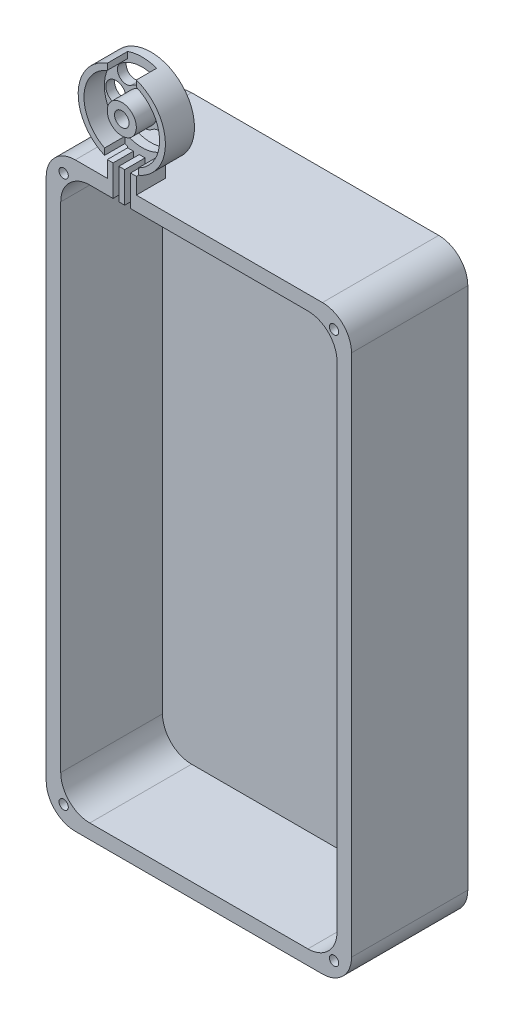
SolidWorks part; units mm, degrees
ref_plane "Front Plane" through (0, 0, 0) normal (0, 0, 1) x (1, 0, 0)
ref_plane "Top Plane" through (0, 0, 0) normal (0, 1, 0) x (1, 0, 0)
ref_plane "Right Plane" through (0, 0, 0) normal (1, 0, 0) x (0, 0, -1)
sketch "Sketch1" plane through (0, 0, 0) normal (0, 0, 1) x (1, 0, 0)
  line L1 (0, 0) -> (105, 0)
  line L2 (0, 0) -> (0, 200)
  line L3 (0, 200) -> (105, 200)
  line L4 (105, 0) -> (105, 200)
  dimension "D1" = 105
  dimension "D2" = 200
extrude "Boss-Extrude1" add sketch "Sketch1" along normal blind 40
sketch "Sketch2" plane through (0, 0, 40) normal (0, 0, 1) x (1, 0, 0)
  line L12 (5, 195) -> (5, 5)
  line L13 (5, 5) -> (100, 5)
  line L14 (100, 5) -> (100, 195)
  line L15 (100, 195) -> (5, 195)
  line L16 (5, 195) -> (5, 5)
  line L17 (5, 5) -> (100, 5)
  line L18 (100, 5) -> (100, 195)
  line L19 (100, 195) -> (5, 195)
  dimension "D1" = 5
extrude "Cut-Extrude1" cut sketch "Sketch2" against normal blind 35
fillet "Fillet1" radius 10 8 edges at (100, 5, 22.5) (105, 0, 20) (0, 0, 20) (5, 5, 22.5) (5, 195, 22.5) (0, 200, 20) (100, 195, 22.5) (105, 200, 20)
sketch "Sketch3" plane through (0, 0, 40) normal (0, 0, 1) x (1, 0, 0)
  line L0 (0, 190) -> (0, 10) construction
  line L1 (95, 200) -> (10, 200) construction
  line L2 (52.5, 200) -> (52.5, 0) construction
  line L3 (10, 0) -> (95, 0) construction
  line L4 (0, 100) -> (105, 100) construction
  line L5 (105, 10) -> (105, 190) construction
  circle A0 centre (6, 194) radius 1.6
  circle A1 centre (99, 194) radius 1.6
  circle A2 centre (99, 6) radius 1.6
  circle A3 centre (6, 6) radius 1.6
  dimension "D1" = 3.2
  dimension "D2" = 6
  dimension "D3" = 6
extrude "Cut-Extrude2" cut sketch "Sketch3" against normal blind 35
sketch "Sketch4" plane through (0, 0, 40) normal (0, 0, 1) x (1, 0, 0)
  line L2 (21, 200) -> (21, 206)
  line L4 (31, 200) -> (31, 206)
  line L5 (0, 190) -> (0, 10) construction
  line L6 (21, 200) -> (31, 200)
  line L7 (95, 200) -> (10, 200) construction
  arc A0 (31, 206) -> (21, 206) centre (26, 220.1421) ccw
  dimension "D4" = 30
  dimension "D1" = 6
  dimension "D2" = 6
  dimension "D3" = 21
  dimension "D5" = 10
extrude "Boss-Extrude2" add sketch "Sketch4" against normal blind 10
sketch "Sketch6" plane through (0, 0, 40) normal (0, 0, 1) x (1, 0, 0)
  circle A0 centre (26, 220.1421) radius 2.5
  dimension "D1" = 5
extrude "Cut-Extrude3" cut sketch "Sketch6" against normal up to surface (10 mm away) up to face at (26, 210.2855, 30)
sketch "Sketch7" plane through (0, 0, 40) normal (0, 0, 1) x (1, 0, 0)
  line L0 (20.966, 234.2722) -> (20.966, 232.1301)
  line L1 (30.966, 232.1562) -> (30.966, 234.2962)
  line L2 (21, 206) -> (21, 208.1421)
  line L3 (31, 206) -> (31, 208.1421)
  circle A0 centre (26, 220.1421) radius 13
  arc A1 (31, 206) -> (21, 206) centre (26, 220.1421) ccw construction
  arc A2 (31, 206) -> (21, 206) centre (26, 220.1421) ccw
  circle A3 centre (26, 220.1421) radius 5
  dimension "D1" = 26
  dimension "D5" = 10
  dimension "D2" = 2.1421
  dimension "D3" = 2.14
  dimension "D4" = 10
extrude "Cut-Extrude5" cut sketch "Sketch7" against normal blind 7 contours A0 A3
sketch "Sketch9" plane through (0, 0, 40) normal (0, 0, 1) x (1, 0, 0)
  line L0 (21, 231.4992) -> (31, 231.4992)
  line L1 (21, 206) -> (31, 206)
  line L2 (21, 231.4992) -> (21, 236.2177)
  line L3 (21, 236.2177) -> (31, 236.2177)
  line L4 (31, 231.4992) -> (31, 236.2177)
  circle A0 centre (26, 220.1421) radius 5 construction
  point P12 (28.9963, 222.2726)
  circle M5 centre (26, 220.1421) radius 13
  arc M24 (31, 206) -> (21, 206) centre (26, 220.1421) ccw
  dimension "D3" = 5
  dimension "D1" = 10
  dimension "D2" = 4.7185
extrude "Cut-Extrude8" cut sketch "Sketch9" against normal blind 7 contours L4 L3 L2 M24 | L0 L4 L2 M5 | L4 L2 M5 M24
sketch "Sketch10" plane through (0, 0, 40) normal (0, 0, 1) x (1, 0, 0)
  line L1 (20.0722, 205.5809) -> (31.7029, 205.5809)
  line L2 (20.0722, 205.5809) -> (20.0722, 209.4312)
  line L3 (20.0722, 209.4312) -> (31.7029, 209.4312)
  line L4 (31.7029, 205.5809) -> (31.7029, 209.4312)
  point P5 (0, 0)
  point P6 (0, 0)
  point P7 (20.0722, 205.7671)
  point P8 (31.7029, 205.5809)
extrude "Cut-Extrude11" cut sketch "Sketch10" against normal blind 7
sketch "Sketch11" plane through (0, 0, 40) normal (0, 0, 1) x (1, 0, 0)
  line L1 (23, 205.7748) -> (25, 205.7748)
  line L2 (23, 205.7748) -> (23, 194.6833)
  line L3 (23, 194.6833) -> (25, 194.6833)
  line L4 (25, 205.7748) -> (25, 194.6833)
  line L6 (27, 205.8743) -> (29, 205.8743)
  line L7 (27, 205.8743) -> (27, 194.718)
  line L8 (27, 194.718) -> (29, 194.718)
  line L9 (29, 205.8743) -> (29, 194.718)
  line L10 (21, 205.5809) -> (21, 200) construction
  line L11 (31, 200) -> (31, 205.5809) construction
  dimension "D1" = 2
  dimension "D2" = 2
  dimension "D3" = 2
  dimension "D4" = 2
  dimension "D5" = 11.0915
  dimension "D6" = 11.1563
extrude "Cut-Extrude12" cut sketch "Sketch11" against normal blind 7
sketch "Sketch12" plane through (0, 0, 30) normal (0, 0, -1) x (-1, 0, 0)
  line L0 (-26, 235.1421) -> (-26, 200) construction
  line L1 (-21, 200) -> (-31, 200) construction
  line L2 (-39, 220.1421) -> (-13, 220.1421) construction
  arc A0 (-21, 206) -> (-31, 206) centre (-26, 220.1421) ccw construction
  arc A1 (-20.5, 227.266) -> (-31.5, 227.266) centre (-26, 220.1421) ccw construction
  circle A2 centre (-26, 220.1421) radius 5 construction
  arc A7 (-18.6667, 229.6407) -> (-33.3333, 229.6407) centre (-26, 220.1421) ccw
  arc A12 (-22.3333, 224.8914) -> (-29.6667, 224.8914) centre (-26, 220.1421) ccw
  circle A13 centre (-26, 220.1421) radius 13 construction
  arc A14 (-22.3333, 224.8914) -> (-18.6667, 229.6407) centre (-20.5, 227.266) ccw
  arc A15 (-33.3333, 229.6407) -> (-29.6667, 224.8914) centre (-31.5, 227.266) ccw
  arc A16 (-20.5, 213.0182) -> (-31.5, 213.0182) centre (-26, 220.1421) cw construction
  arc A17 (-18.6667, 210.6436) -> (-33.3333, 210.6436) centre (-26, 220.1421) cw
  arc A18 (-22.3333, 215.3929) -> (-29.6667, 215.3929) centre (-26, 220.1421) cw
  arc A19 (-22.3333, 215.3929) -> (-18.6667, 210.6436) centre (-20.5, 213.0182) cw
  arc A20 (-33.3333, 210.6436) -> (-29.6667, 215.3929) centre (-31.5, 213.0182) cw
  point P12 (-26, 229.1421)
  point P21 (-26, 211.1421)
  dimension "D1" = 10
  dimension "D2" = 26
  dimension "D4" = 12
  dimension "D5" = 3
  dimension "D3" = 5.5
extrude "Cut-Extrude13" cut sketch "Sketch12" against normal blind 7
sketch "Sketch13" plane through (0, 0, 30) normal (0, 0, -1) x (-1, 0, 0)
  line L0 (-41, 220.1421) -> (-11, 220.1421) construction
  line L1 (-26, 235.1421) -> (-26, 200) construction
  line L2 (-21, 200) -> (-31, 200) construction
  arc A0 (-21, 206) -> (-31, 206) centre (-26, 220.1421) ccw construction
  circle A1 centre (-17, 220.1421) radius 3.5
  circle A2 centre (-35, 220.1421) radius 3.5
  circle A3 centre (-26, 220.1421) radius 13 construction
  point P12 (-26, 220.1421)
  dimension "D1" = 7
  dimension "D3" = 26
  dimension "D2" = 9
extrude "Cut-Extrude14" cut sketch "Sketch13" against normal blind 7
